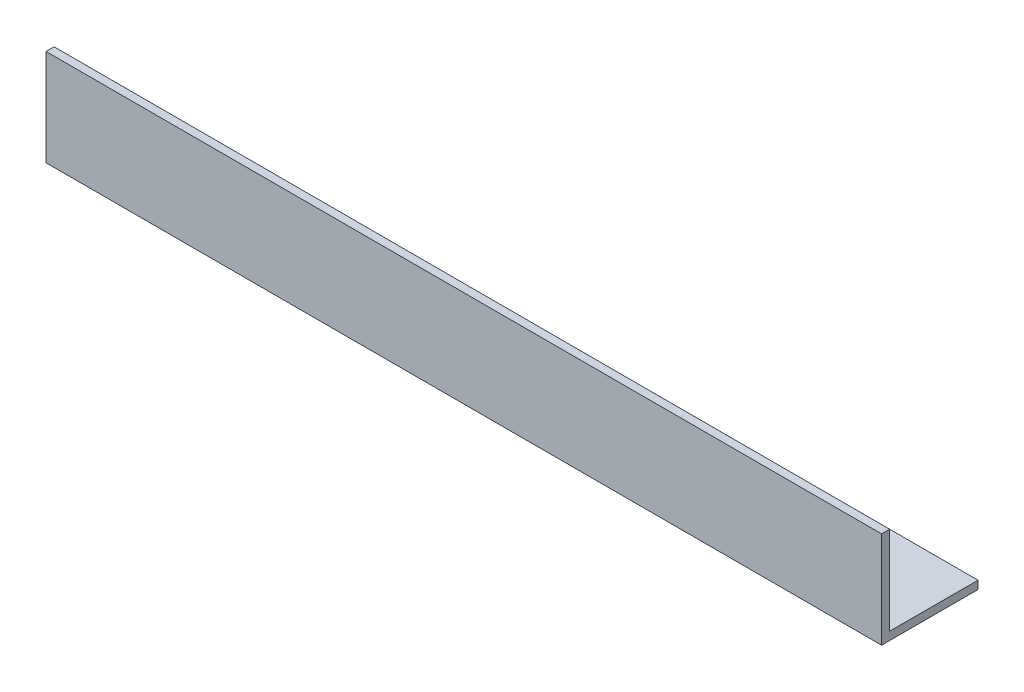
SolidWorks part; units mm, degrees
material "6061-T6 (SS)"
ref_plane "Front Plane" through (0, 0, 0) normal (0, 0, 1) x (1, 0, 0)
ref_plane "Top Plane" through (0, 0, 0) normal (0, 1, 0) x (1, 0, 0)
ref_plane "Right Plane" through (0, 0, 0) normal (1, 0, 0) x (0, 0, -1)
sketch "Sketch1" plane through (0, 0, 0) normal (1, 0, 0) x (0, 0, -1)
  line L0 (0, 0) -> (0, 19.05)
  line L1 (0, 19.05) -> (1.6002, 19.05)
  line L2 (1.6002, 19.05) -> (1.6002, 1.6002)
  line L3 (1.6002, 1.6002) -> (19.05, 1.6002)
  line L4 (19.05, 1.6002) -> (19.05, 0)
  line L5 (19.05, 0) -> (0, 0)
  dimension "D1" = 19.05
  dimension "D2" = 1.6002
extrude "Boss-Extrude1" add sketch "Sketch1" along normal blind 165.1
